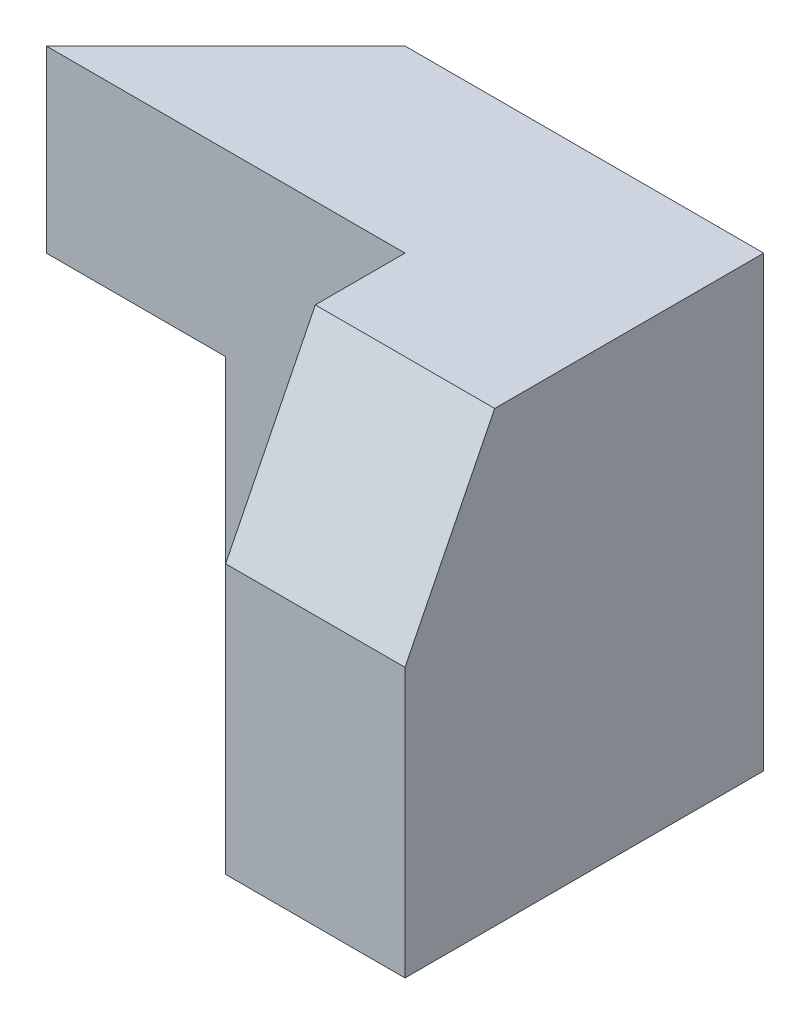
SolidWorks part; units mm, degrees
ref_plane "Front Plane" through (0, 0, 0) normal (0, 0, 1) x (1, 0, 0)
ref_plane "Top Plane" through (0, 0, 0) normal (0, 1, 0) x (1, 0, 0)
ref_plane "Right Plane" through (0, 0, 0) normal (1, 0, 0) x (0, 0, -1)
sketch "Sketch1" plane through (0, 0, 0) normal (0, 0, 1) x (1, 0, 0)
  line L1 (0, 0) -> (30, 0)
  line L2 (0, 0) -> (0, 25)
  line L3 (0, 25) -> (30, 25)
  line L4 (30, 0) -> (30, 25)
  dimension "D1" = 30
  dimension "D2" = 25
extrude "Boss-Extrude1" add sketch "Sketch1" along normal blind 20
sketch "Sketch2" plane through (0, 0, 20) normal (0, 0, 1) x (1, 0, 0)
  line L0 (30, 25) -> (0, 25) construction
  line L1 (0, 0) -> (20, 0)
  line L2 (0, 0) -> (0, 25)
  line L3 (0, 25) -> (20, 25)
  line L4 (20, 0) -> (20, 25)
  dimension "D1" = 20
extrude "Cut-Extrude1" cut sketch "Sketch2" against normal blind 10
sketch "Sketch3" plane through (20, 0, 0) normal (-1, 0, 0) x (0, 0, 1)
  line L0 (15, 25) -> (20, 15)
  line L1 (10, 25) -> (20, 25) construction
  line L2 (20, 0) -> (20, 25) construction
  line L3 (20, 15) -> (20, 25)
  line L4 (20, 25) -> (15, 25)
  dimension "D1" = 5
  dimension "D2" = 10
extrude "Cut-Extrude2" cut sketch "Sketch3" against normal blind 20
sketch "Sketch4" plane through (0, 25, 0) normal (0, 1, 0) x (1, 0, 0)
  line L0 (0, -10) -> (10, -10)
  line L1 (20, -10) -> (0, -10) construction
  line L2 (10, -10) -> (0, 0)
  line L3 (0, 0) -> (0, -10)
  dimension "D1" = 10
extrude "Cut-Extrude3" cut sketch "Sketch4" against normal blind 40
sketch "Sketch5" plane through (20, 0, 0) normal (-1, 0, 0) x (0, 0, 1)
  line L0 (10, 0) -> (10, 25) construction
  line L1 (10, 15) -> (-10, 15)
  line L2 (10, 15) -> (10, 25)
  line L3 (10, 25) -> (-10, 25)
  line L4 (-10, 15) -> (-10, 25)
  dimension "D1" = 10
  dimension "D2" = 20
extrude "Cut-Extrude4" cut sketch "Sketch5" along normal blind 20
sketch "Sketch6" plane through (0, 15, 0) normal (0, 1, 0) x (1, 0, 0)
  line L1 (0, -10) -> (20, -10)
  line L2 (20, -10) -> (20, 0)
  line L3 (0, 0) -> (20, 0) construction
  line L4 (20, 0) -> (10, 0)
  line L5 (10, 0) -> (0, -10)
  dimension "D1" = 10
  dimension "D2" = 20
extrude "Boss-Extrude2" add sketch "Sketch6" along normal blind 10
